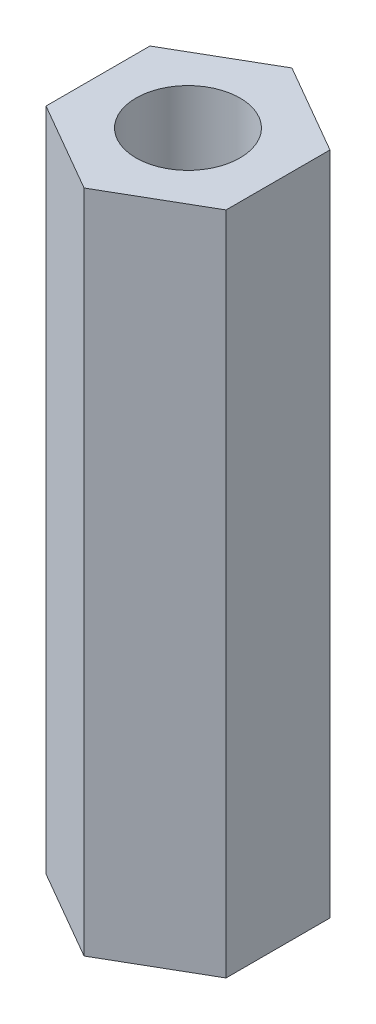
SolidWorks part; units mm, degrees
ref_plane "Face" through (0, 0, 0) normal (0, 0, 1) x (1, 0, 0)
ref_plane "Dessus" through (0, 0, 0) normal (0, 1, 0) x (1, 0, 0)
ref_plane "Droite" through (0, 0, 0) normal (1, 0, 0) x (0, 0, -1)
sketch "Esquisse1" plane through (0, 0, 0) normal (0, 1, 0) x (1, 0, 0)
  line L0 (0, 0) -> (0, 5.5688) construction
  line L1 (0, 5) -> (-4.3301, 2.5)
  line L2 (-4.3301, 2.5) -> (-4.3301, -2.5)
  line L3 (-4.3301, -2.5) -> (0, -5)
  line L4 (0, -5) -> (4.3301, -2.5)
  line L5 (4.3301, -2.5) -> (4.3301, 2.5)
  line L6 (4.3301, 2.5) -> (0, 5)
  circle A0 centre (0, 0) radius 4.3301 construction
  circle A1 centre (0, 0) radius 2.5
  dimension "D1" = 10
  dimension "D2" = 5
extrude "Extrusion1" add sketch "Esquisse1" along normal blind 32
